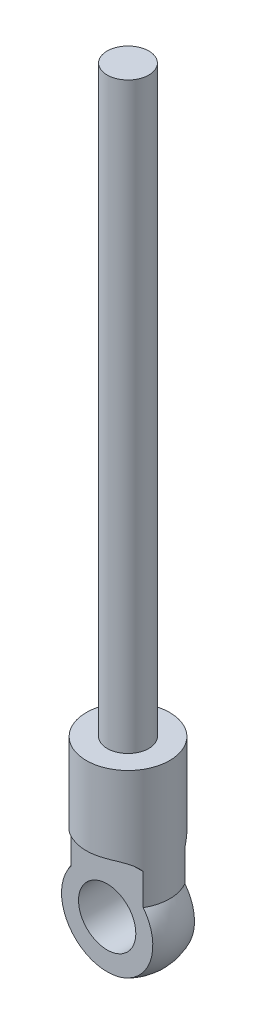
SolidWorks part; units mm, degrees
material "1060 Alloy"
ref_plane "Front Plane" through (0, 0, 0) normal (0, 0, 1) x (1, 0, 0)
ref_plane "Top Plane" through (0, 0, 0) normal (0, 1, 0) x (1, 0, 0)
ref_plane "Right Plane" through (0, 0, 0) normal (1, 0, 0) x (0, 0, -1)
sketch "Sketch1" plane through (0, 0, 0) normal (0, 0, 1) x (1, 0, 0)
  line L0 (0, 0) -> (0, 56)
  line L1 (0, 0) -> (0, -19)
  line L2 (0, 56) -> (-2, 56)
  line L3 (-2, 56) -> (-2, 0)
  line L4 (-2, 0) -> (-4, 0)
  line L5 (-4, 0) -> (-4, -11.5)
  line L6 (-12.3945, -19) -> (12.915, -19) construction
  arc A1 (0, -19) -> (-4, -11.5) centre (0, -14.1833) cw
  dimension "D1" = 56
  dimension "D2" = 19
  dimension "D3" = 2
  dimension "D4" = 2
  dimension "D5" = 11.5
revolve "Revolve1" add sketch "Sketch1" angle 360 about L0
sketch "Sketch2" plane through (0, 0, 0) normal (1, 0, 0) x (0, 0, -1)
  line L0 (-4, 0) -> (-4, -7.5)
  line L1 (-4, 0) -> (-4, -11.5) construction
  line L2 (-2, -7.5) -> (-2, -18.5651)
  line L3 (0, 0) -> (0, -19) construction
  line L4 (2, -7.5) -> (2, -18.5651)
  line L5 (4, -11.5) -> (-4, -11.5) construction
  line L6 (4, -7.5) -> (4, 0)
  line L7 (4, 0) -> (-4, 0)
  line L8 (4, -8.078) -> (4, -7.5)
  line L11 (-4, -8.078) -> (-4, -7.5)
  arc A0 (-4, -11.5) -> (4, -11.5) centre (0, -14.1833) ccw construction
  arc A1 (-4, -7.5) -> (-2, -11.5) centre (-4, -10) cw
  arc A2 (4, -7.5) -> (2, -11.5) centre (4, -10) ccw
  arc A3 (4, -8.078) -> (2, -18.5651) centre (0, -12.7494) cw
  arc A4 (-4, -8.078) -> (-2, -18.5651) centre (0, -12.7494) ccw
  dimension "D3" = 6.15
  dimension "D1" = 7.5
  dimension "D2" = 4
extrude "Cut-Extrude1" cut sketch "Sketch2" against normal blind 10 and the other way through all contours L11 A4 L2 A1 | A3 L8 A2 L4
sketch "Sketch3" plane through (0, 0, 2) normal (0, 0, 1) x (1, 0, 0)
  line L0 (0, 0) -> (0, -18.5651) construction
  arc A0 (-3.4641, -11.5) -> (3.4641, -11.5) centre (0, -14.1833) ccw construction
  circle A1 centre (0, -14) radius 2.75
  dimension "D1" = 5.5
  dimension "D2" = 14
extrude "Cut-Extrude2" cut sketch "Sketch3" against normal through all and the other way through all
sketch "Sketch4" plane through (0, 0, 0) normal (0, 0, 1) x (1, 0, 0)
  circle A0 centre (0, -14) radius 2.75 construction
  circle A1 centre (0, -14) radius 2.75
